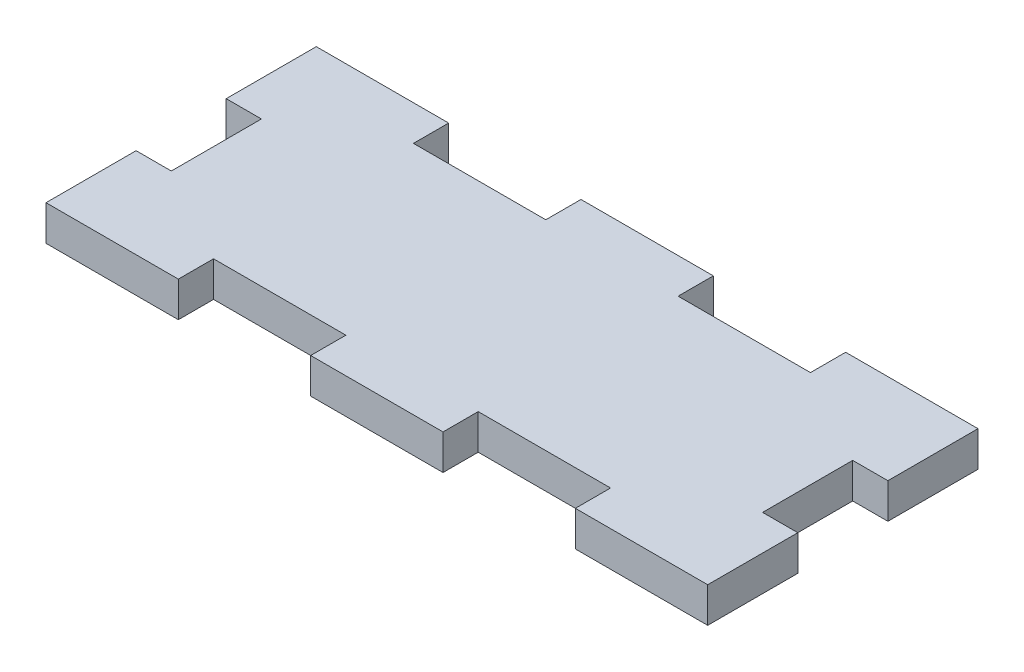
SolidWorks part; units mm, degrees
ref_plane "Front Plane" through (0, 0, 0) normal (0, 0, 1) x (1, 0, 0)
ref_plane "Top Plane" through (0, 0, 0) normal (0, 1, 0) x (1, 0, 0)
ref_plane "Right Plane" through (0, 0, 0) normal (1, 0, 0) x (0, 0, -1)
sketch "Sketch1" plane through (0, 0, 0) normal (0, 1, 0) x (1, 0, 0)
  line L1 (-29.845, -12.192) -> (29.845, -12.192)
  line L2 (-29.845, -12.192) -> (-29.845, 12.192)
  line L3 (-29.845, 12.192) -> (29.845, 12.192)
  line L4 (29.845, -12.192) -> (29.845, 12.192)
  line L5 (-29.845, -12.192) -> (29.845, 12.192) construction
  line L6 (-29.845, 12.192) -> (29.845, -12.192) construction
  point P0 (0, 0)
  dimension "D1" = 59.69
  dimension "D2" = 24.384
extrude "Boss-Extrude2" add sketch "Sketch1" along normal blind 3.175
sketch "Sketch3" plane through (0, 3.175, 0) normal (0, 1, 0) x (1, 0, 0)
  line L0 (29.845, 12.192) -> (-29.845, 12.192) construction
  line L1 (-5.969, 9.017) -> (5.969, 9.017) construction
  line L2 (-5.969, 9.017) -> (-5.969, 15.367) construction
  line L3 (-5.969, 15.367) -> (5.969, 15.367) construction
  line L4 (5.969, 9.017) -> (5.969, 15.367) construction
  line L5 (-5.969, 9.017) -> (5.969, 15.367) construction
  line L6 (-5.969, 15.367) -> (5.969, 9.017) construction
  line L7 (-29.845, -12.192) -> (29.845, -12.192) construction
  line L8 (5.969, 9.017) -> (17.907, 9.017)
  line L9 (5.969, 9.017) -> (5.969, 12.192)
  line L10 (5.969, 12.192) -> (17.907, 12.192)
  line L11 (17.907, 9.017) -> (17.907, 12.192)
  line L12 (5.969, -12.192) -> (17.907, -12.192)
  line L13 (5.969, -12.192) -> (5.969, -9.017)
  line L14 (5.969, -9.017) -> (17.907, -9.017)
  line L15 (17.907, -12.192) -> (17.907, -9.017)
  point P0 (0, 12.192)
  dimension "D1" = 6.35
  dimension "D2" = 11.938
  dimension "D3" = 11.938
  dimension "D4" = 3.175
extrude "Cut-Extrude2" cut sketch "Sketch3" against normal blind 3.175
pattern_linear "LPattern2" count 2 spacing 23.876 along (-1, 0, 0) of "Cut-Extrude2"
sketch "Sketch4" plane through (0, 3.175, 0) normal (0, 1, 0) x (1, 0, 0)
  line L0 (-29.845, 12.192) -> (-29.845, -12.192) construction
  line L1 (-33.02, -4.064) -> (-26.67, -4.064)
  line L2 (-33.02, -4.064) -> (-33.02, 4.064)
  line L3 (-33.02, 4.064) -> (-26.67, 4.064)
  line L4 (-26.67, -4.064) -> (-26.67, 4.064)
  line L5 (-33.02, -4.064) -> (-26.67, 4.064) construction
  line L6 (-33.02, 4.064) -> (-26.67, -4.064) construction
  line L8 (29.845, -12.192) -> (29.845, 12.192) construction
  line L9 (26.67, -4.064) -> (33.02, -4.064)
  line L10 (26.67, -4.064) -> (26.67, 4.064)
  line L11 (26.67, 4.064) -> (33.02, 4.064)
  line L12 (33.02, -4.064) -> (33.02, 4.064)
  line L13 (26.67, -4.064) -> (33.02, 4.064) construction
  line L14 (26.67, 4.064) -> (33.02, -4.064) construction
  point P0 (-29.845, 0)
  point P7 (29.845, 0)
  dimension "D1" = 8.128
  dimension "D2" = 6.35
  dimension "D3" = 6.35
extrude "Cut-Extrude3" cut sketch "Sketch4" against normal blind 3.175
